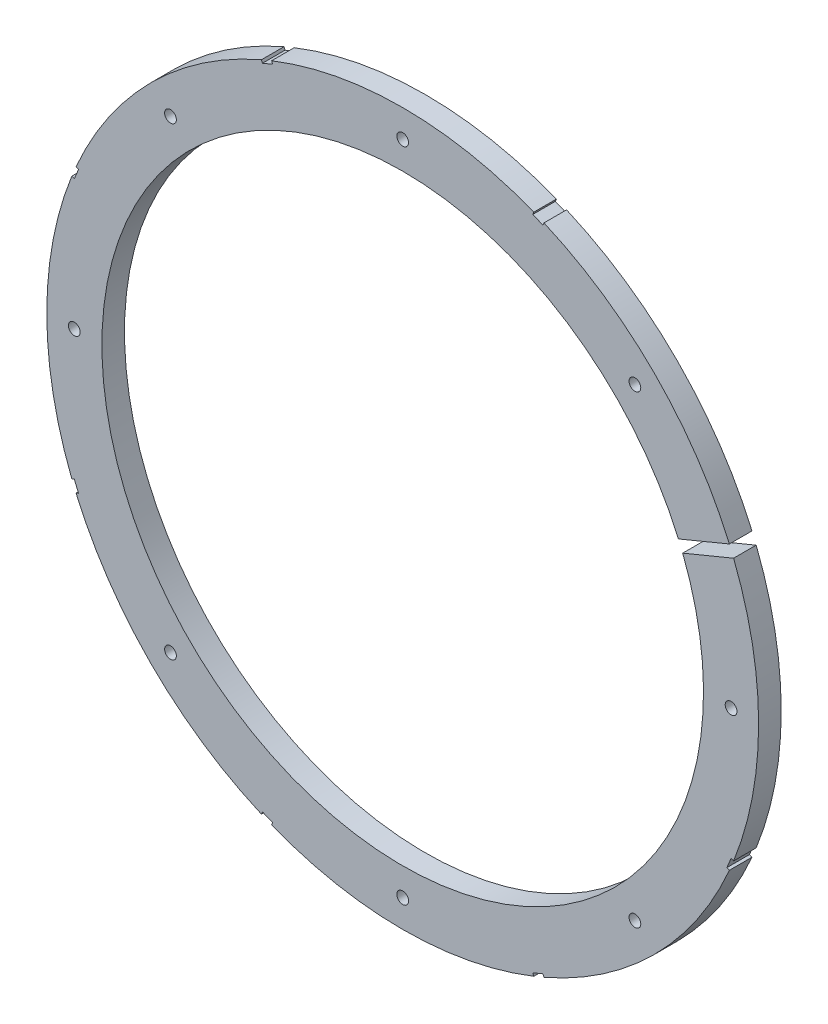
SolidWorks part; units mm, degrees
material "Brass"
ref_plane "Front Plane" through (0, 0, 0) normal (0, 0, 1) x (1, 0, 0)
ref_plane "Top Plane" through (0, 0, 0) normal (0, 1, 0) x (1, 0, 0)
ref_plane "Right Plane" through (0, 0, 0) normal (1, 0, 0) x (0, 0, -1)
sketch "Sketch4" plane through (0, 0, 0) normal (0, 0, 1) x (1, 0, 0)
  circle A0 centre (0, 0) radius 82.042
  dimension "D1" = 164.084
extrude "Boss-Extrude2" add sketch "Sketch4" along normal blind 5.207
sketch "Sketch5" plane through (0, 0, 5.207) normal (0, 0, 1) x (1, 0, 0)
  circle A0 centre (0, 0) radius 69.342
  circle A1 centre (0, 0) radius 82.042 construction
  dimension "D1" = 12.7
extrude "Cut-Extrude5" cut sketch "Sketch5" against normal through all
sketch "Sketch8" plane through (0, 0, 5.207) normal (0, 0, 1) x (1, 0, 0)
  line L0 (81.7642, 35.2425) -> (62.991, 27.4664)
  line L1 (81.7642, 35.2425) -> (82.7362, 32.8958)
  line L2 (62.991, 27.4664) -> (63.963, 25.1197)
  line L3 (82.7362, 32.8958) -> (63.963, 25.1197)
  line L4 (81.7642, 35.2425) -> (63.963, 25.1197) construction
  line L5 (62.991, 27.4664) -> (82.7362, 32.8958) construction
  line L6 (0, 0) -> (50.4438, 0) construction
  line L7 (32.8124, 75.8976) -> (30.4658, 76.8696)
  line L8 (32.8124, 75.8976) -> (32.3264, 74.7243)
  line L9 (30.4658, 76.8696) -> (29.9798, 75.6963)
  line L10 (32.3264, 74.7243) -> (29.9798, 75.6963)
  line L11 (30.4658, 76.8696) -> (32.3264, 74.7243) construction
  line L12 (32.8124, 75.8976) -> (29.9798, 75.6963) construction
  line L13 (-30.4658, 76.8696) -> (-32.8124, 75.8976)
  line L14 (-30.4658, 76.8696) -> (-29.9798, 75.6963)
  line L15 (-29.9798, 75.6963) -> (-32.3264, 74.7243)
  line L16 (-32.8124, 75.8976) -> (-32.3264, 74.7243)
  line L17 (-30.4658, 76.8696) -> (-32.3264, 74.7243) construction
  line L18 (-32.8124, 75.8976) -> (-29.9798, 75.6963) construction
  line L19 (-75.8976, 32.8124) -> (-76.8696, 30.4658)
  line L20 (-75.8976, 32.8124) -> (-74.7243, 32.3264)
  line L21 (-74.7243, 32.3264) -> (-75.6963, 29.9798)
  line L22 (-76.8696, 30.4658) -> (-75.6963, 29.9798)
  line L23 (-75.8976, 32.8124) -> (-75.6963, 29.9798) construction
  line L24 (-76.8696, 30.4658) -> (-74.7243, 32.3264) construction
  line L25 (-76.8696, -30.4658) -> (-75.8976, -32.8124)
  line L26 (-76.8696, -30.4658) -> (-75.6963, -29.9798)
  line L27 (-75.6963, -29.9798) -> (-74.7243, -32.3264)
  line L28 (-75.8976, -32.8124) -> (-74.7243, -32.3264)
  line L29 (-76.8696, -30.4658) -> (-74.7243, -32.3264) construction
  line L30 (-75.8976, -32.8124) -> (-75.6963, -29.9798) construction
  line L31 (-32.8124, -75.8976) -> (-30.4658, -76.8696)
  line L32 (-32.8124, -75.8976) -> (-32.3264, -74.7243)
  line L33 (-32.3264, -74.7243) -> (-29.9798, -75.6963)
  line L34 (-30.4658, -76.8696) -> (-29.9798, -75.6963)
  line L35 (-32.8124, -75.8976) -> (-29.9798, -75.6963) construction
  line L36 (-30.4658, -76.8696) -> (-32.3264, -74.7243) construction
  line L37 (30.4658, -76.8696) -> (32.8124, -75.8976)
  line L38 (30.4658, -76.8696) -> (29.9798, -75.6963)
  line L39 (29.9798, -75.6963) -> (32.3264, -74.7243)
  line L40 (32.8124, -75.8976) -> (32.3264, -74.7243)
  line L41 (30.4658, -76.8696) -> (32.3264, -74.7243) construction
  line L42 (32.8124, -75.8976) -> (29.9798, -75.6963) construction
  line L43 (75.8976, -32.8124) -> (76.8696, -30.4658)
  line L44 (75.8976, -32.8124) -> (74.7243, -32.3264)
  line L45 (74.7243, -32.3264) -> (75.6963, -29.9798)
  line L46 (76.8696, -30.4658) -> (75.6963, -29.9798)
  line L47 (75.8976, -32.8124) -> (75.6963, -29.9798) construction
  line L48 (76.8696, -30.4658) -> (74.7243, -32.3264) construction
  circle A0 centre (0, 0) radius 69.342 construction
  circle A1 centre (0, 0) radius 82.042 construction
  point P1 (72.8636, 30.1811)
  point P3 (31.3961, 75.7969)
  point P11 (-31.3961, 75.7969)
  point P20 (-75.7969, 31.3961)
  point P25 (-75.7969, -31.3961)
  point P26 (0, 0)
  point P31 (-31.3961, -75.7969)
  point P36 (31.3961, -75.7969)
  point P41 (75.7969, -31.3961)
  point P46 (0, 0)
  dimension "D1" = 20.32
  dimension "D2" = 9.525
  dimension "D3" = 2.54
  dimension "D4" = 22.5
  dimension "D5" = 1.27
  dimension "D6" = 2.54
  dimension "D7" = 1.27
  dimension "D8" = 1.27
  dimension "D9" = 0.635
  dimension "D10" = 67.5
  dimension "D12" = 0.635
  dimension "D13" = 22.5
  dimension "D14" = 0.635
  dimension "D11" = 7
extrude "Cut-Extrude11" cut sketch "Sketch8" against normal through all
hole_wizard "#6-32 Tapped Hole1" positions "Sketch10" profile "Sketch9" tap size "#6-32" standard "ANSI Inch" end condition through all
sketch "Sketch10" plane through (0, 0, 5.207) normal (0, 0, 1) x (1, 0, 0)
  line L0 (0, 0) -> (75.692, 0) construction
  line L2 (0, 0) -> (53.5223, 53.5223) construction
  line L4 (0, 0) -> (53.5223, -53.5223) construction
  circle A0 centre (0, 0) radius 69.342 construction
  point P0 (75.692, 0)
  point P10 (53.5223, -53.5223)
  point P11 (0, -75.692)
  point P12 (-53.5223, -53.5223)
  point P13 (-75.692, 0)
  point P14 (-53.5223, 53.5223)
  point P15 (0, 75.692)
  point P16 (53.5223, 53.5223)
  dimension "D1" = 6.35
  dimension "D3" = 45
  dimension "D4" = 45
  dimension "D5" = 6.35
  dimension "D2" = 8
cosmetic thread "Hole Thread1" parameters "D2"=3.5052
cosmetic thread "Hole Thread2" parameters "D2"=3.5052
cosmetic thread "Hole Thread3" parameters "D2"=3.5052
cosmetic thread "Hole Thread4" parameters "D2"=3.5052
cosmetic thread "Hole Thread5" parameters "D2"=3.5052
cosmetic thread "Hole Thread6" parameters "D2"=3.5052
cosmetic thread "Hole Thread7" parameters "D2"=3.5052
cosmetic thread "Hole Thread8" parameters "D2"=3.5052
sketch "Sketch9" plane through (75.692, 0, 5.207) normal (1, 0, 0) x (0, -1, 0)
  line L0 (0, 0) -> (0, 5.207)
  line L1 (0, 5.207) -> (1.3525, 5.207)
  line L2 (1.3525, 5.207) -> (1.3525, 0)
  line L5 (1.3525, 0) -> (0, 0)
  line L11 (0, -6.35) -> (0, 107.95) construction
  dimension "Thru Tap Drill Dia." = 2.7051
  dimension "Thru Tap Drill Depth" = 5.207
